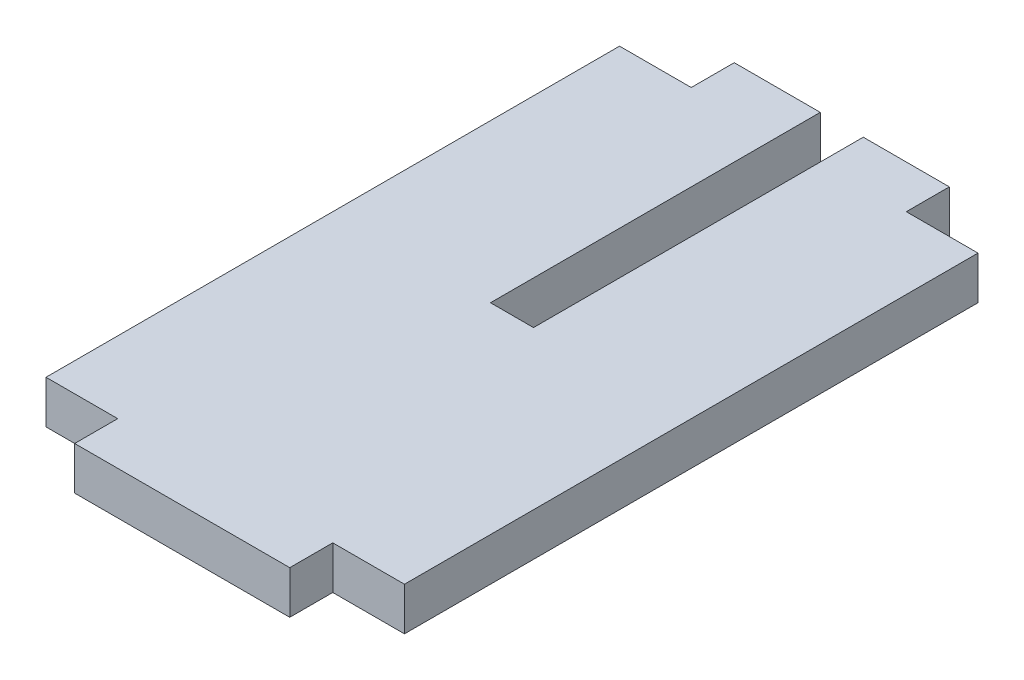
SolidWorks part; units mm, degrees
ref_plane "Front Plane" through (0, 0, 0) normal (0, 0, 1) x (1, 0, 0)
ref_plane "Top Plane" through (0, 0, 0) normal (0, 1, 0) x (1, 0, 0)
ref_plane "Right Plane" through (0, 0, 0) normal (1, 0, 0) x (0, 0, -1)
sketch "Sketch1" plane through (0, 0, 0) normal (0, 1, 0) x (1, 0, 0)
  line L0 (-25, 40) -> (-15, 40)
  line L1 (-15, -46) -> (15, -46)
  line L2 (-25, -40) -> (-25, 40)
  line L3 (-15, 46) -> (15, 46)
  line L4 (25, -40) -> (25, 40)
  line L7 (-15, 40) -> (-15, 46)
  line L8 (15, 46) -> (15, 40)
  line L9 (15, 40) -> (25, 40)
  line L10 (-25, -40) -> (-15, -40)
  line L11 (-15, -40) -> (-15, -46)
  line L12 (15, -40) -> (15, -46)
  line L13 (15, -40) -> (25, -40)
  point P0 (0, 0)
  point P1 (0, 46)
  point P2 (0, -46)
  point P3 (25, 0)
  point P4 (-25, 0)
  dimension "D1" = 30
  dimension "D2" = 50
  dimension "D3" = 6
  dimension "D4" = 92
extrude "Boss-Extrude1" add sketch "Sketch1" along normal blind 6
sketch "Sketch2" plane through (0, 6, 0) normal (0, 1, 0) x (1, 0, 0)
  line L0 (15, 46) -> (-15, 46) construction
  line L1 (-3, 0) -> (3, 0)
  line L2 (-3, 0) -> (-3, 46)
  line L3 (-3, 46) -> (3, 46)
  line L4 (3, 0) -> (3, 46)
  point P6 (0, 0)
  dimension "D1" = 6
extrude "Cut-Extrude1" cut sketch "Sketch2" against normal through all
